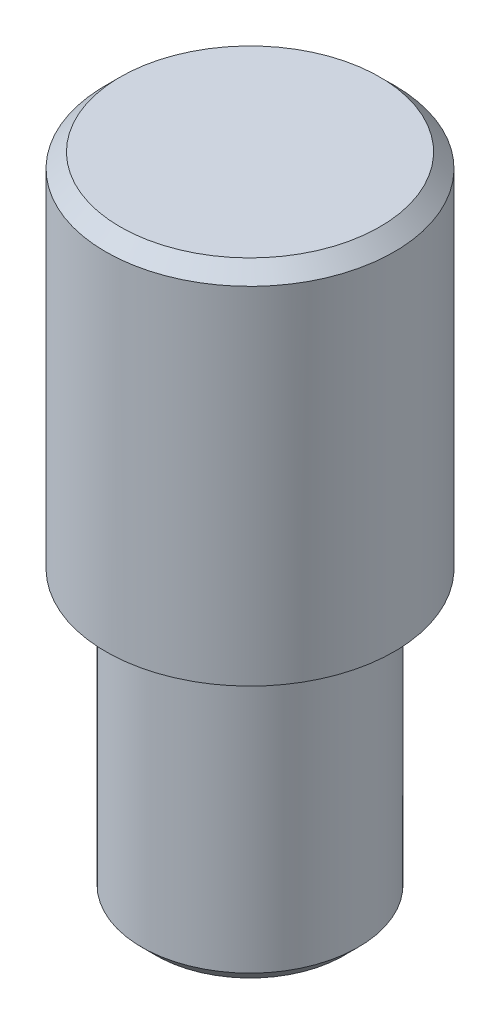
SolidWorks part; units mm, degrees
ref_plane "前视基准面" through (0, 0, 0) normal (0, 0, 1) x (1, 0, 0)
ref_plane "上视基准面" through (0, 0, 0) normal (0, 1, 0) x (1, 0, 0)
ref_plane "右视基准面" through (0, 0, 0) normal (1, 0, 0) x (0, 0, -1)
sketch "草图1" plane through (0, 0, 0) normal (0, 0, 1) x (1, 0, 0)
  line L0 (0, 0) -> (10, 0)
  line L1 (10, 0) -> (10, -25)
  line L2 (10, -25) -> (7.5, -25)
  line L3 (7.5, -25) -> (7.5, -45)
  line L4 (7.5, -45) -> (0, -45)
  line L5 (0, -45) -> (0, 0)
  dimension "D1" = 10
  dimension "D2" = 7.5
  dimension "D3" = 20
  dimension "D4" = 45
revolve "旋转1" add sketch "草图1" angle 360 about L5
chamfer "倒角1" distance 1 angle 45 2 edges at (0, 0, -10) (0, -45, -7.5)
ref_plane "基准面1" through (0, 0, 6.5) normal (0, 0, 1) x (1, 0, 0)
sketch "草图2" plane through (0, 0, 6.5) normal (0, 0, 1) x (1, 0, 0)
  line L0 (0, -1) -> (0, -25) construction
  line L1 (-10, -1) -> (10, -1) construction
  line L2 (-10, -25) -> (10, -25) construction
  line L3 (0, -5) -> (0, -20) construction
  line L4 (9, 0) -> (-9, 0) construction
  line L5 (3, -5) -> (3, -20)
  line L6 (-3, -5) -> (-3, -20)
  arc A0 (3, -5) -> (-3, -5) centre (0, -5) ccw
  arc A1 (-3, -20) -> (3, -20) centre (0, -20) ccw
  point P10 (0, -12.5)
  dimension "D1" = 3
  dimension "D2" = 15
  dimension "D3" = 5
extrude "切除-拉伸1" [suppressed] cut sketch "草图2" along normal through all
